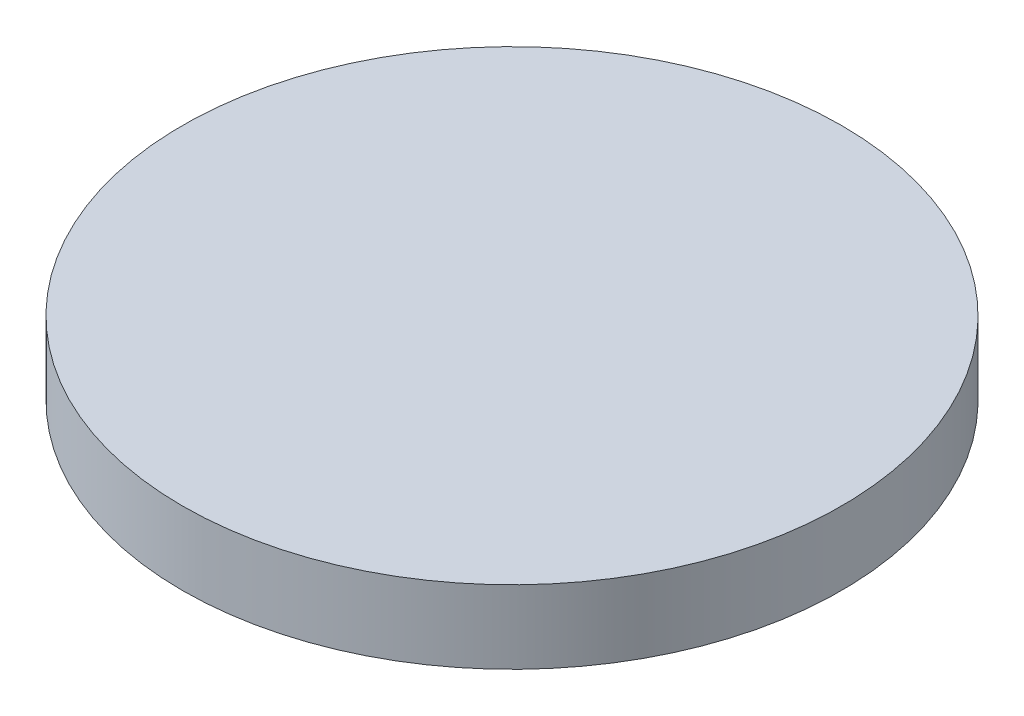
SolidWorks part; units mm, degrees
ref_plane "Front Plane" through (0, 0, 0) normal (0, 0, 1) x (1, 0, 0)
ref_plane "Top Plane" through (0, 0, 0) normal (0, 1, 0) x (1, 0, 0)
ref_plane "Right Plane" through (0, 0, 0) normal (1, 0, 0) x (0, 0, -1)
sketch "Sketch2" plane through (0, 0, 0) normal (0, 1, 0) x (1, 0, 0)
  circle A0 centre (0, 0) radius 45
extrude "Boss-Extrude1" add sketch "Sketch2" along normal blind 10
